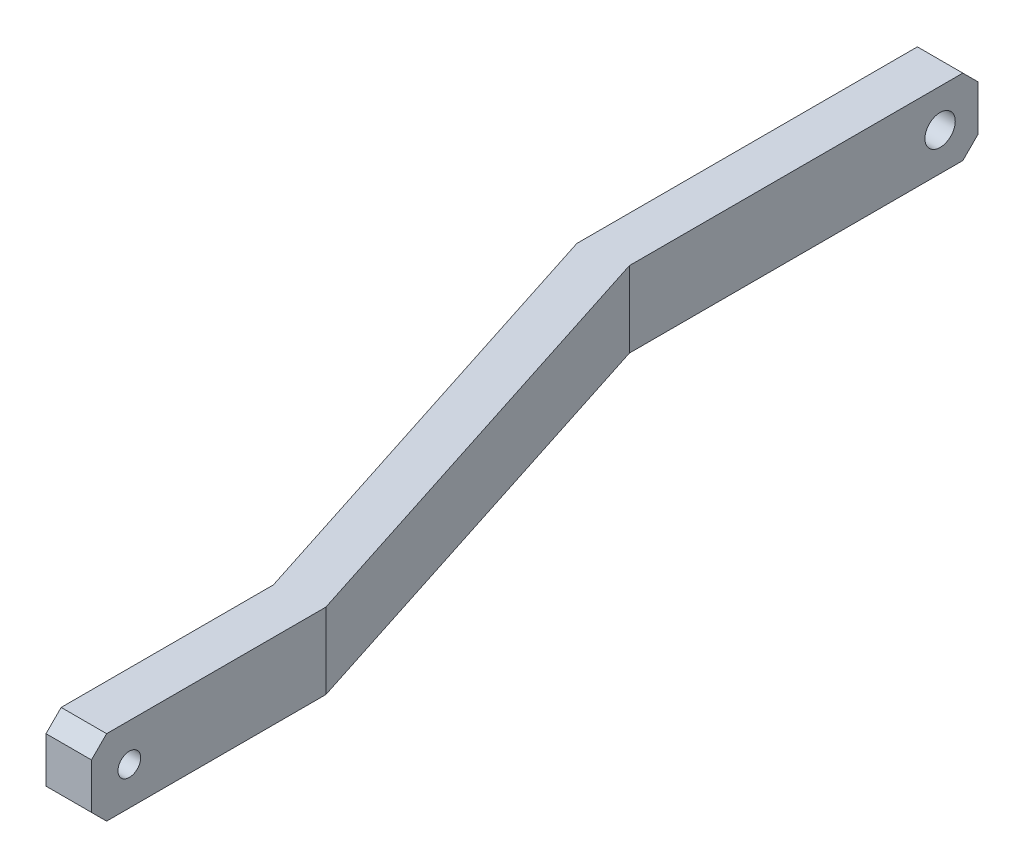
SolidWorks part; units mm, degrees
ref_plane "Front Plane" through (0, 0, 0) normal (0, 0, 1) x (1, 0, 0)
ref_plane "Top Plane" through (0, 0, 0) normal (0, 1, 0) x (1, 0, 0)
ref_plane "Right Plane" through (0, 0, 0) normal (1, 0, 0) x (0, 0, -1)
sketch "Sketch2" plane through (0, 0, 0) normal (0, 1, 0) x (1, 0, 0)
  line L0 (0, 0) -> (0, 15.4707)
  line L1 (0, 15.4707) -> (-9.5, 45)
  line L2 (-9.5, 45) -> (-9.5, 68)
  line L3 (-9.5, 68) -> (-12.5, 68)
  line L4 (-12.5, 68) -> (-12.5, 44.5293)
  line L5 (-12.5, 44.5293) -> (-3, 15)
  line L6 (-3, 15) -> (-3, 0)
  line L7 (-3, 0) -> (0, 0)
  line L8 (-7.75, 29.7647) -> (-4.8942, 30.6834) construction
  dimension "D1" = 3
  dimension "D2" = 6.5
  dimension "D3" = 68
  dimension "D4" = 30
  dimension "D5" = 15
extrude "Boss-Extrude1" add sketch "Sketch2" along normal blind 5
sketch "Sketch3" plane through (-3, 0, 0) normal (-1, 0, 0) x (0, 0, 1)
  line L0 (-2.5, 2.5) -> (0, 2.5) construction
  line L1 (0, 5) -> (0, 0) construction
  circle A0 centre (-2.5, 2.5) radius 0.75
  dimension "D1" = 1.5
  dimension "D2" = 2.5
extrude "Cut-Extrude1" cut sketch "Sketch3" against normal through all
sketch "Sketch4" plane through (-9.5, 0, 0) normal (1, 0, 0) x (0, 0, -1)
  line L0 (65.5, 2.5) -> (68, 2.5) construction
  line L1 (68, 5) -> (68, 0) construction
  circle A0 centre (65.5, 2.5) radius 1
  dimension "D2" = 2
  dimension "D1" = 2.5
extrude "Cut-Extrude2" cut sketch "Sketch4" against normal through all
chamfer "Chamfer1" distance 1 angle 45 4 edges at (-1.5, 0, 0) (-1.5, 5, 0) (-11, 5, -68) (-11, 0, -68)
